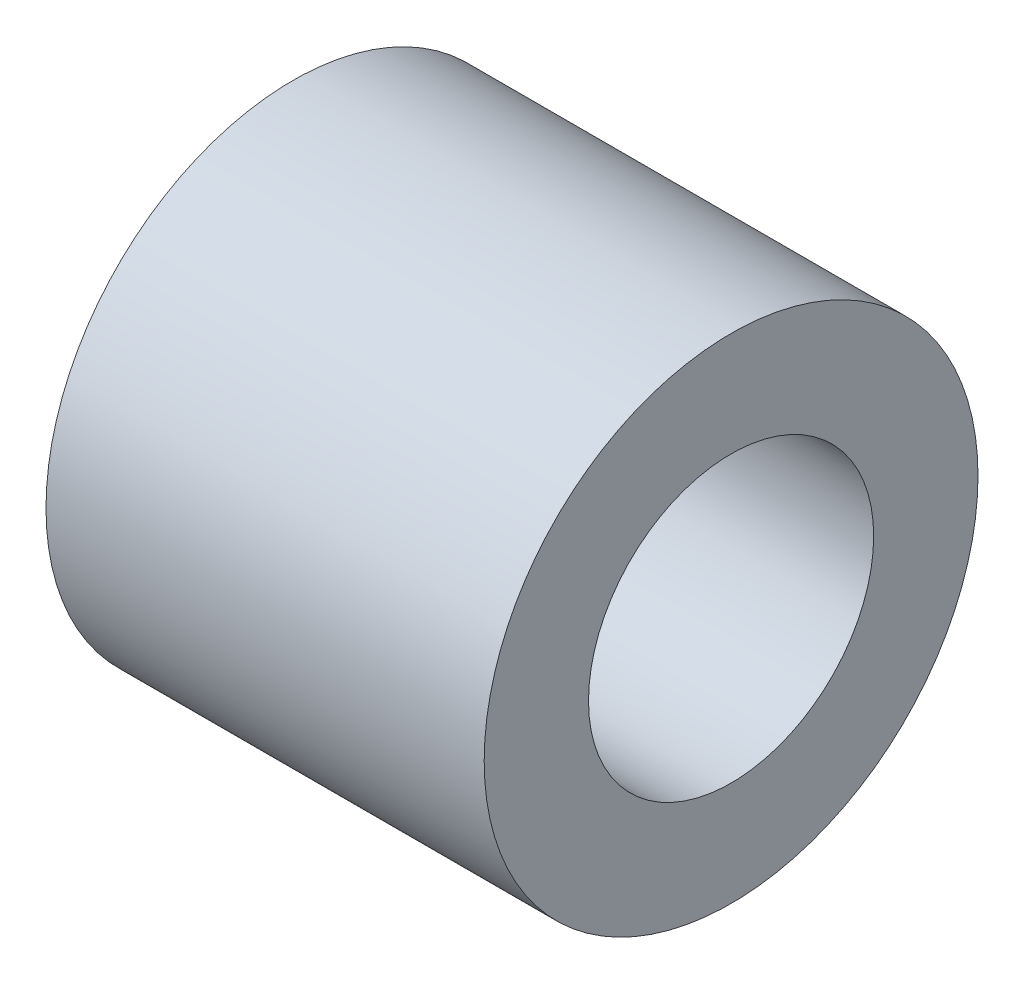
SolidWorks part; units mm, degrees
material "ABS"
ref_plane "Front Plane" through (0, 0, 0) normal (0, 0, 1) x (1, 0, 0)
ref_plane "Top Plane" through (0, 0, 0) normal (0, 1, 0) x (1, 0, 0)
ref_plane "Right Plane" through (0, 0, 0) normal (1, 0, 0) x (0, 0, -1)
sketch "Sketch1" plane through (0, 0, 0) normal (0, 1, 0) x (1, 0, 0)
  line L0 (0, 0) -> (22.4144, 0) construction
  line L1 (0, 0) -> (12.6, 0)
  line L2 (0, 0) -> (0, -4.1)
  line L3 (0, -4.1) -> (12.6, -4.1)
  line L4 (12.6, 0) -> (12.6, -4.1)
  line L5 (0, 0) -> (12.6, 0)
  line L6 (0, 0) -> (0, -7.1)
  line L7 (0, -7.1) -> (12.6, -7.1)
  line L8 (12.6, 0) -> (12.6, -7.1)
  dimension "D1" = 12.6
  dimension "D2" = 4.1
  dimension "D3" = 3
revolve "Revolve1" add sketch "Sketch1" angle 360 about L0
